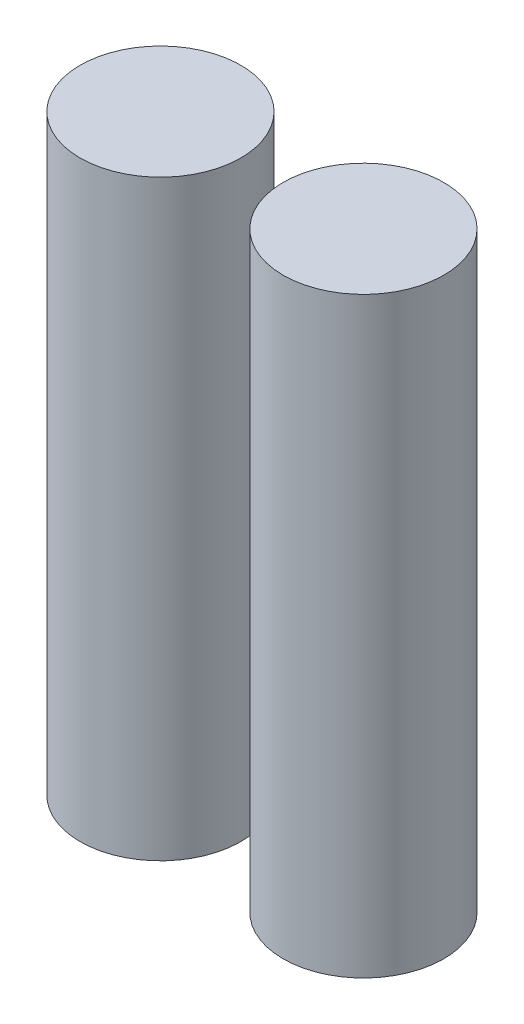
SolidWorks part; units mm, degrees
ref_plane "Front Plane" through (0, 0, 0) normal (0, 0, 1) x (1, 0, 0)
ref_plane "Top Plane" through (0, 0, 0) normal (0, 1, 0) x (1, 0, 0)
ref_plane "Right Plane" through (0, 0, 0) normal (1, 0, 0) x (0, 0, -1)
sketch "Sketch2" plane through (0, 0, 0) normal (0, 1, 0) x (1, 0, 0)
  circle A0 centre (-12, 0) radius 9.5
  circle A1 centre (12, 0) radius 9.5
extrude "Boss-Extrude1" add sketch "Sketch2" along normal blind 70 contours A1 | A0
